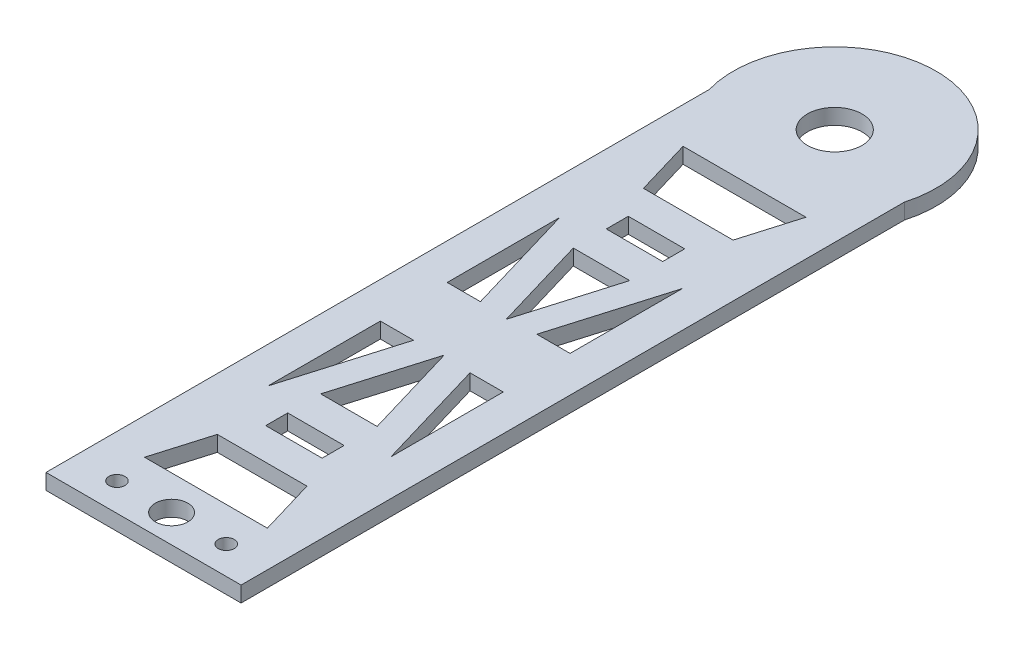
SolidWorks part; units mm, degrees
material "6061-T6 (SS)"
ref_plane "Front Plane" through (0, 0, 0) normal (0, 0, 1) x (1, 0, 0)
ref_plane "Top Plane" through (0, 0, 0) normal (0, 1, 0) x (1, 0, 0)
ref_plane "Right Plane" through (0, 0, 0) normal (1, 0, 0) x (0, 0, -1)
sketch "Sketch2" plane through (0, 0, 0) normal (0, 1, 0) x (1, 0, 0)
  line L0 (-12.5, 42.5) -> (12.5, 42.5) construction
  line L1 (-12.5, -42.5) -> (12.5, -42.5)
  line L2 (-12.5, -42.5) -> (-12.5, 42.5)
  line L3 (0, 46.0707) -> (0, -42.5) construction
  line L4 (12.5, -42.5) -> (12.5, 42.5)
  line L5 (12.5, 0) -> (-12.5, 0) construction
  arc A0 (12.5, 42.5) -> (-12.5, 42.5) centre (0, 46.0707) ccw
  dimension "D3" = 13
  dimension "D1" = 85
  dimension "D2" = 25
extrude "Boss-Extrude1" add sketch "Sketch2" along normal blind 2
sketch "Sketch4" plane through (0, 0, 0) normal (0, -1, 0) x (1, 0, 0)
  line L0 (0, -59.0707) -> (0, 42.5) construction
  line L1 (-12.5, 42.5) -> (12.5, 42.5) construction
  arc A0 (-12.5, -42.5) -> (12.5, -42.5) centre (0, -46.0707) ccw construction
  point P5 (0, 0)
  point P9 (0, 42.5)
sketch "Sketch5" plane through (0, 0, 0) normal (0, 1, 0) x (1, 0, 0)
  line L0 (0, 59.0707) -> (0, -42.5) construction
  line L1 (0, 34.507) -> (7.8731, 34.507)
  line L2 (7.8731, 34.507) -> (5.7424, 27.3032)
  line L3 (5.7424, 27.3032) -> (0, 27.3032)
  line L4 (0, 27.3032) -> (0, 34.507)
  line L5 (0, 23.2314) -> (3.6148, 23.2314)
  line L6 (3.6148, 23.2314) -> (3.6148, 20.4125)
  line L7 (3.6148, 20.4125) -> (0, 20.4125)
  line L8 (0, 20.4125) -> (0, 23.2314)
  line L10 (0, 16.1842) -> (3.6148, 16.1842)
  line L11 (3.6148, 16.1842) -> (0, 3.9625)
  line L12 (0, 3.9625) -> (0, 16.1842)
  line L13 (7.8731, 18.6899) -> (3.6148, 4.2822)
  line L14 (3.6148, 4.2822) -> (7.8731, 4.2822)
  line L15 (7.8731, 4.2822) -> (7.8731, 18.6899)
  point P13 (0, 91.4137)
  point P18 (0, 0)
  point P20 (0, 49.9272)
  point P21 (0, 0)
extrude "Cut-Extrude4" cut sketch "Sketch5" along normal up to next (2 mm away)
mirror "Mirror1" about plane through (0, 0, 0) normal (1, 0, 0) of "Cut-Extrude4"
mirror "Mirror3" about plane through (0, 0, 0) normal (0, 0, 1) of "Mirror1", "Cut-Extrude4"
sketch "Sketch6" plane through (0, 0, 0) normal (0, 1, 0) x (1, 0, 0)
  line L0 (0, 59.0707) -> (0, -42.5) construction
  circle A0 centre (0, 46.0707) radius 3.5
  arc A1 (12.5, 42.5) -> (-12.5, 42.5) centre (0, 46.0707) ccw construction
  dimension "D1" = 7
extrude "Cut-Extrude5" cut sketch "Sketch6" along normal through all both and the other way through all
sketch "Sketch8" plane through (0, 0, 0) normal (0, 1, 0) x (1, 0, 0)
  line L0 (0, 59.0707) -> (0, -42.5) construction
  circle A0 centre (0, -38.9041) radius 2.0841
  circle A1 centre (7, -38.9041) radius 1.0224
  circle A2 centre (-7, -38.9041) radius 1.0224
  point P6 (0, 0)
  point P9 (0, 0)
  dimension "D1" = 7
  dimension "D2" = 7
extrude "Cut-Extrude7" cut sketch "Sketch8" along normal up to next
